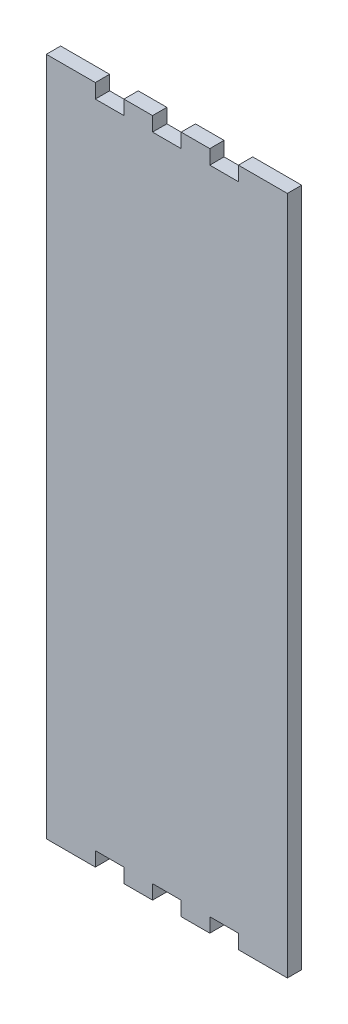
SolidWorks part; units mm, degrees
ref_plane "Front Plane" through (0, 0, 0) normal (0, 0, 1) x (1, 0, 0)
ref_plane "Top Plane" through (0, 0, 0) normal (0, 1, 0) x (1, 0, 0)
ref_plane "Right Plane" through (0, 0, 0) normal (1, 0, 0) x (0, 0, -1)
sketch "Model" plane through (0, 0, 0) normal (0, 0, 1) x (1, 0, 0)
  line L679 (980.6539, 22.8602) -> (994.5047, 22.8602)
  line L680 (994.5047, 22.8602) -> (994.5047, 28.5752)
  line L681 (994.5047, 28.5752) -> (1005.9354, 28.5752)
  line L682 (1005.9354, 28.5752) -> (1005.9354, 22.8602)
  line L683 (1005.9354, 22.8602) -> (1017.3661, 22.8602)
  line L684 (1017.3661, 22.8602) -> (1017.3661, 28.5752)
  line L685 (1017.3661, 28.5752) -> (1028.7968, 28.5752)
  line L686 (1028.7968, 28.5752) -> (1028.7968, 22.8602)
  line L687 (1028.7968, 22.8602) -> (1040.224, 22.8602)
  line L688 (1040.224, 22.8602) -> (1040.224, 28.5752)
  line L689 (1040.224, 28.5752) -> (1051.6547, 28.5752)
  line L690 (1051.6547, 28.5752) -> (1051.6547, 22.8602)
  line L691 (1051.6547, 22.8602) -> (1065.5091, 22.8602)
  line L692 (1065.5091, 22.8602) -> (1071.2209, 22.8602)
  line L693 (1071.2209, 22.8602) -> (1071.2209, 28.5752)
  line L694 (1071.2209, 28.5752) -> (1071.2209, 288.5754)
  line L695 (1071.2209, 288.5754) -> (1071.2209, 294.2904)
  line L696 (1071.2209, 294.2904) -> (1065.5091, 294.2904)
  line L697 (1065.5091, 294.2904) -> (1051.6547, 294.2904)
  line L698 (1051.6547, 294.2904) -> (1051.6547, 288.5754)
  line L699 (1051.6547, 288.5754) -> (1040.224, 288.5754)
  line L700 (1040.224, 288.5754) -> (1040.224, 294.2904)
  line L701 (1040.224, 294.2904) -> (1028.7968, 294.2904)
  line L702 (1028.7968, 294.2904) -> (1028.7968, 288.5754)
  line L703 (1028.7968, 288.5754) -> (1017.3661, 288.5754)
  line L704 (1017.3661, 288.5754) -> (1017.3661, 294.2904)
  line L705 (1017.3661, 294.2904) -> (1005.9354, 294.2904)
  line L706 (1005.9354, 294.2904) -> (1005.9354, 288.5754)
  line L707 (1005.9354, 288.5754) -> (994.5047, 288.5754)
  line L708 (994.5047, 288.5754) -> (994.5047, 294.2904)
  line L709 (994.5047, 294.2904) -> (980.6539, 294.2904)
  line L710 (980.6539, 294.2904) -> (974.9385, 294.2904)
  line L711 (974.9385, 294.2904) -> (974.9385, 288.5754)
  line L712 (974.9385, 288.5754) -> (974.9385, 28.5752)
  line L713 (974.9385, 28.5752) -> (974.9385, 22.8602)
  line L714 (974.9385, 22.8602) -> (980.6539, 22.8602)
extrude "Boss-Extrude1" add sketch "Model" along normal blind 5.715
